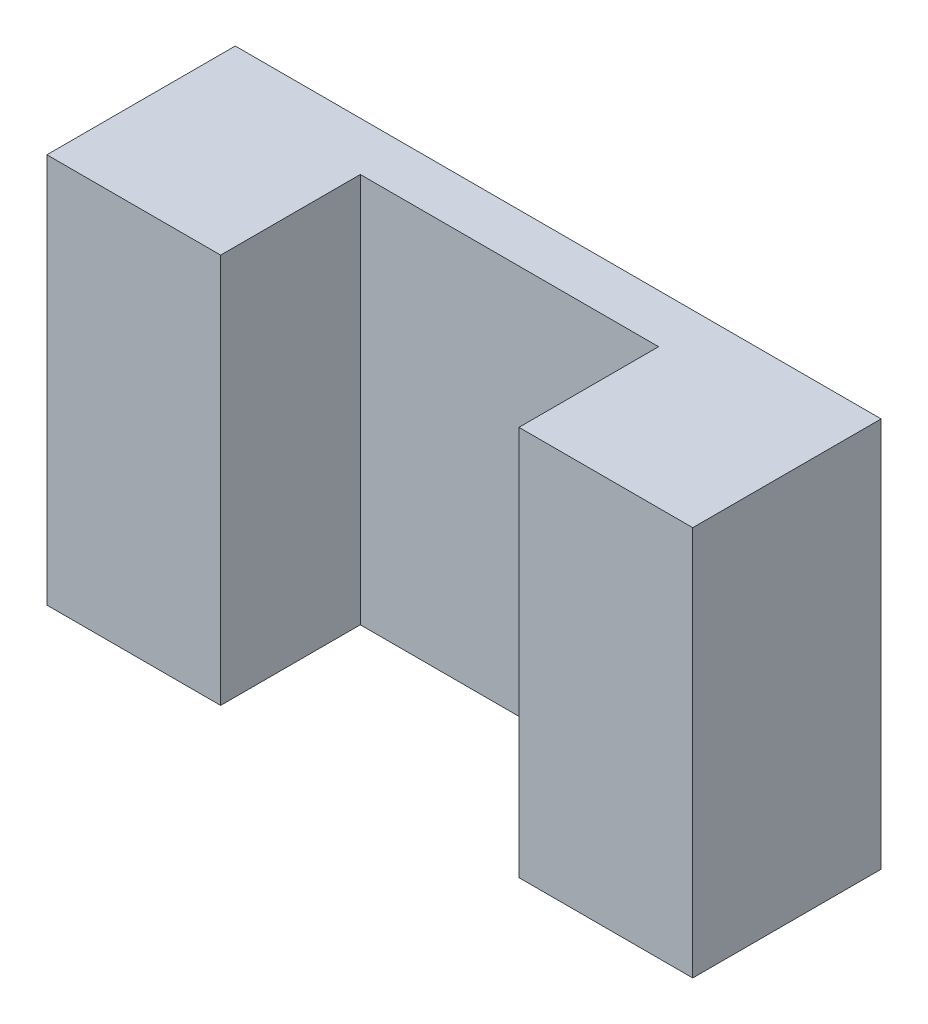
SolidWorks part; units mm, degrees
material "ABS"
ref_plane "Front Plane" through (0, 0, 0) normal (0, 0, 1) x (1, 0, 0)
ref_plane "Top Plane" through (0, 0, 0) normal (0, 1, 0) x (1, 0, 0)
ref_plane "Right Plane" through (0, 0, 0) normal (1, 0, 0) x (0, 0, -1)
sketch "Sketch1" plane through (0, 0, 0) normal (0, 0, 1) x (1, 0, 0)
  line L1 (32.9969, 19.925) -> (-32.9969, 19.925)
  line L2 (32.9969, 19.925) -> (32.9969, -19.925)
  line L3 (32.9969, -19.925) -> (-32.9969, -19.925)
  line L4 (-32.9969, 19.925) -> (-32.9969, -19.925)
  line L5 (32.9969, 19.925) -> (-32.9969, -19.925) construction
  line L6 (32.9969, -19.925) -> (-32.9969, 19.925) construction
  point P0 (0, 0)
  dimension "D1" = 39.85
  dimension "D2" = 65.9938
extrude "Boss-Extrude1" add sketch "Sketch1" along normal blind 20
sketch "Sketch2" plane through (0, 0, 20) normal (0, 0, 1) x (1, 0, 0)
  line L0 (-32.9969, -19.925) -> (32.9969, -19.925) construction
  line L1 (15.24, 19.925) -> (-15.24, 19.925)
  line L2 (15.24, 19.925) -> (15.24, -19.925)
  line L3 (15.24, -19.925) -> (-15.24, -19.925)
  line L4 (-15.24, 19.925) -> (-15.24, -19.925)
  line L5 (15.24, 19.925) -> (-15.24, -19.925) construction
  line L6 (15.24, -19.925) -> (-15.24, 19.925) construction
  point P0 (0, 0)
  dimension "D1" = 30.48
extrude "Cut-Extrude1" cut sketch "Sketch2" against normal blind 15.02
sketch "Sketch3" plane through (0, 0, 20) normal (0, 0, 1) x (1, 0, 0)
  line L1 (-32.9969, 19.925) -> (32.9969, 19.925)
  line L2 (-32.9969, 19.925) -> (-32.9969, -19.925)
  line L3 (-32.9969, -19.925) -> (32.9969, -19.925)
  line L4 (32.9969, 19.925) -> (32.9969, -19.925)
extrude "Cut-Extrude2" cut sketch "Sketch3" against normal blind 0.75
